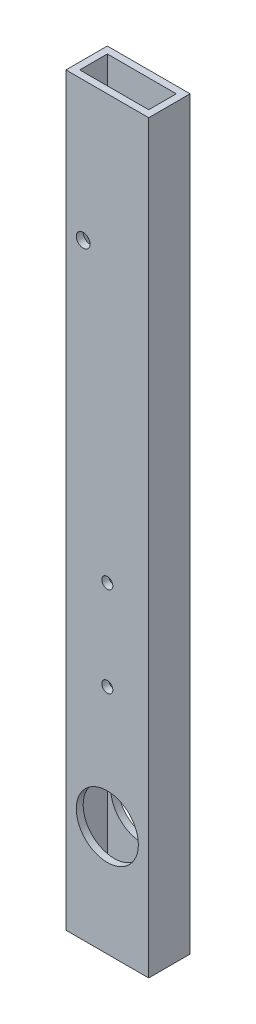
SolidWorks part; units mm, degrees
ref_plane "Front Plane" through (0, 0, 0) normal (0, 0, 1) x (1, 0, 0)
ref_plane "Top Plane" through (0, 0, 0) normal (0, 1, 0) x (1, 0, 0)
ref_plane "Right Plane" through (0, 0, 0) normal (1, 0, 0) x (0, 0, -1)
sketch "Sketch1" plane through (0, 0, 0) normal (0, 1, 0) x (1, 0, 0)
  line L0 (3.175, 15.875) -> (34.925, 15.875)
  line L1 (0, 0) -> (38.1, 0)
  line L2 (0, 0) -> (0, 19.05)
  line L3 (0, 19.05) -> (38.1, 19.05)
  line L4 (38.1, 0) -> (38.1, 19.05)
  line L5 (34.925, 3.175) -> (34.925, 15.875)
  line L6 (3.175, 3.175) -> (34.925, 3.175)
  line L7 (3.175, 3.175) -> (3.175, 15.875)
  dimension "D1" = 38.1
  dimension "D2" = 19.05
extrude "Boss-Extrude1" add sketch "Sketch1" along normal blind 342.9
sketch "Sketch2" plane through (0, 0, 0) normal (0, 0, 1) x (1, 0, 0)
  line L0 (19.05, 0) -> (19.05, 50.8) construction
  line L1 (0, 0) -> (38.1, 0) construction
  circle A0 centre (19.05, 50.8) radius 14.2875
  dimension "D1" = 50.8
extrude "Cut-Extrude1" cut sketch "Sketch2" against normal through all
sketch "Sketch3" plane through (0, 0, -19.05) normal (0, 0, -1) x (-1, 0, 0)
  circle A0 centre (-19.05, 106.5419) radius 2.54 construction
  circle A1 centre (-19.05, 106.5419) radius 2.54
  circle A2 centre (-19.05, 147.9963) radius 2.54 construction
  circle A3 centre (-19.05, 147.9963) radius 2.54
  circle A4 centre (-7.9467, 278.9813) radius 3.175 construction
  circle A5 centre (-7.9467, 278.9813) radius 3.175
extrude "Cut-Extrude2" cut sketch "Sketch3" against normal through all
